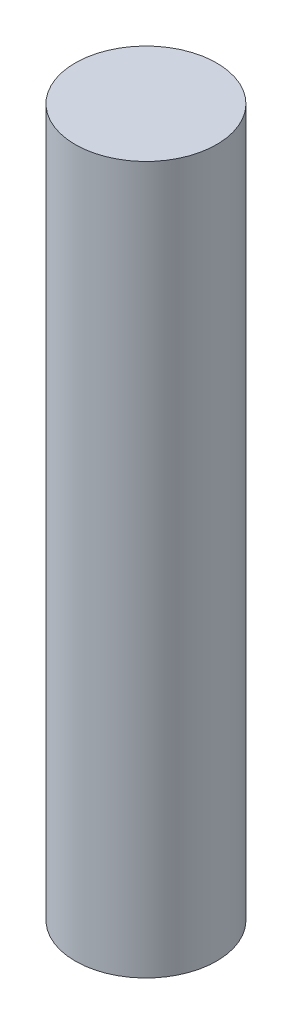
SolidWorks part; units mm, degrees
ref_plane "Front Plane" through (0, 0, 0) normal (0, 0, 1) x (1, 0, 0)
ref_plane "Top Plane" through (0, 0, 0) normal (0, 1, 0) x (1, 0, 0)
ref_plane "Right Plane" through (0, 0, 0) normal (1, 0, 0) x (0, 0, -1)
sketch "Sketch3" plane through (0, 0, 0) normal (0, 1, 0) x (1, 0, 0)
  circle A0 centre (0, 0) radius 3
  dimension "D1" = 6
extrude "Boss-Extrude1" add sketch "Sketch3" along normal blind 30
